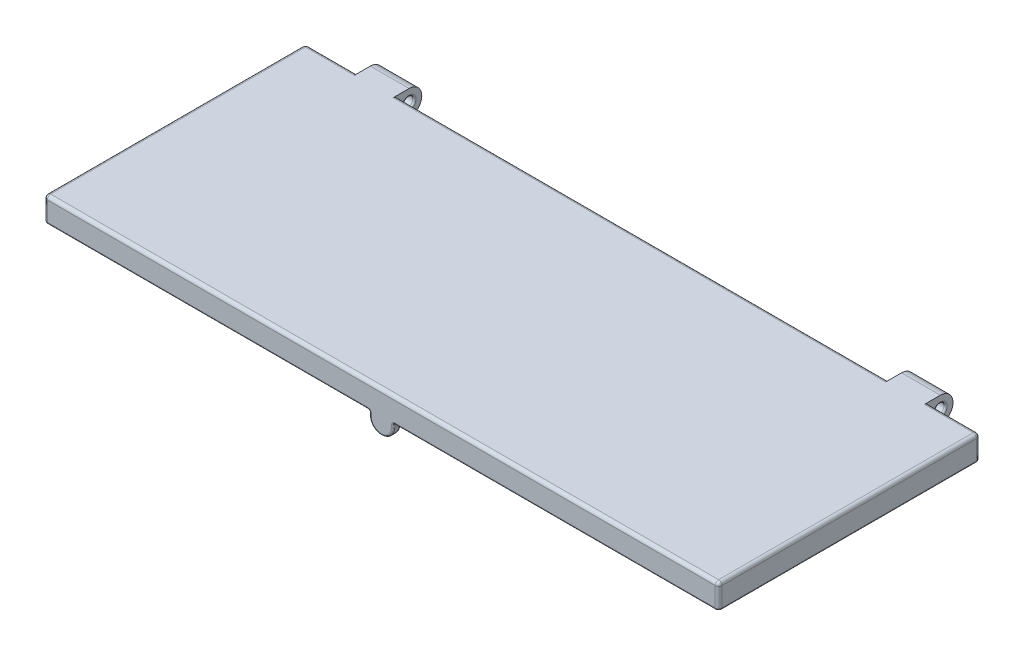
SolidWorks part; units mm, degrees
ref_plane "前视基准面" through (0, 0, 0) normal (0, 0, 1) x (1, 0, 0)
ref_plane "上视基准面" through (0, 0, 0) normal (0, 1, 0) x (1, 0, 0)
ref_plane "右视基准面" through (0, 0, 0) normal (1, 0, 0) x (0, 0, -1)
other "Configuration Table"
sketch "草图1" plane through (0, 0, 0) normal (0, 1, 0) x (1, 0, 0)
  line L0 (160, 61.2) -> (160, 0.8) construction
  line L1 (0, 0) -> (160, 0)
  line L2 (0, 0) -> (0, 62)
  line L3 (0, 62) -> (160, 62)
  line L4 (160, 0) -> (160, 62)
  line L5 (157.6, 62) -> (150.4, 62) construction
extrude "凸台-拉伸1" add sketch "草图1" along normal blind 4
ref_plane "基准面-对称" through (80, 0, 0) normal (1, 0, 0) x (0, 0, -1)
ref_plane "基准面1" through (147.6, 0, 0) normal (-1, 0, 0) x (0, 0, 1)
sketch "草图2" plane through (147.6, 0, 0) normal (-1, 0, 0) x (0, 0, 1)
  line L0 (-62, 4) -> (-65, 4)
  line L1 (-62, 0) -> (-62.6, -0.8)
  line L2 (-62, 0) -> (-62, 4)
  circle A0 centre (-65, 1) radius 1.25
  circle A1 centre (-65, 1) radius 3
  dimension "D1" = 2.5
  dimension "D2" = 6
extrude "凸台-拉伸2" add sketch "草图2" along normal blind 9.2 contours A1 L2 L0 | A1 A0 | A1 L1 L2
mirror "镜向1" about plane through (80, 0, 0) normal (1, 0, 0) of "凸台-拉伸2"
sketch "草图3" plane through (0, 0, 0) normal (0, -1, 0) x (1, 0, 0)
  line L0 (160, 0) -> (160, -62) construction
  line L1 (0, 0) -> (160, 0) construction
  line L2 (0, -62) -> (0, 0) construction
  line L3 (160, 0) -> (160, -62)
  line L4 (0, 0) -> (160, 0)
  line L5 (0, -62) -> (0, 0)
  line L6 (0, -62) -> (1.8, -62)
  line L7 (12.4, -62) -> (0, -62) construction
  line L8 (1.8, -62) -> (1.8, -1.8)
  line L9 (1.8, -1.8) -> (158.2, -1.8)
  line L10 (158.2, -1.8) -> (158.2, -62)
  line L11 (160, -62) -> (147.6, -62) construction
  line L12 (158.2, -62) -> (160, -62)
  dimension "D1" = 1.8
  dimension "D2" = 1.8
extrude "凸台-拉伸3" add sketch "草图3" along normal blind 1.8
sketch "草图4" plane through (0, 0, 0) normal (0, 0, 1) x (1, 0, 0)
  line L0 (80, -1.8) -> (80, -2.8) construction
  line L1 (160, -1.8) -> (0, -1.8) construction
  line L2 (77.2, -2.8) -> (77.2, -1.8)
  line L3 (77.2, -1.8) -> (82.8, -1.8)
  line L4 (82.8, -1.8) -> (82.8, -2.8)
  arc A0 (77.2, -2.8) -> (82.8, -2.8) centre (80, -2.8) ccw
  dimension "D1" = 2.8
  dimension "D2" = 1
extrude "凸台-拉伸4" add sketch "草图4" against normal up to surface (1.8 mm away) up to face at (80, -0.9, -1.8)
sketch "草图5" plane through (0, 0, -1.8) normal (0, 0, -1) x (-1, 0, 0)
  circle A0 centre (-80, -3) radius 0.6
  dimension "D1" = 1.2
extrude "切除-拉伸1" cut sketch "草图5" against normal blind 0.4
fillet "圆角1" radius 0.8 10 edges at (160, 4, -31) (80, 4, -62) (153.8, 4, -62) (6.2, 4, -62) (0, 4, -31) (0, 1.1, -62) (160, 1.1, -62) (160, 1.1, 0) (0, 1.1, 0) (80, 4, 0)
fillet "圆角2" radius 0.4 36 edges at (80, 0, -62) (138.4, 1, -63.75) (147.6, 1, -63.75) (7.1, 0, -62) (12.4, 1, -63.75) (21.6, 1, -63.75) (152.9, 0, -62) (1.8, 0, -31.9) (1.8, -0.9, -62) (80, 0, -1.8) (1.8, -0.9, -1.8) (158.2, 0, -31.9) (158.2, -0.9, -1.8) (158.2, -0.9, -62) (1.8, -1.8, -31.9) (39.5, -1.8, -1.8) (158.2, -1.8, -31.9) (158.7, -1.8, -62) (39, -1.8, 0) (120.5, -1.8, -1.8) (77.2, -1.8, -0.9) (82.8, -1.8, -0.9) (80, -5.6, 0) (82.8, -2.3, 0) (77.2, -2.3, 0) (80, -5.6, -1.8) (77.2, -2.3, -1.8) (82.8, -2.3, -1.8) (121, -1.8, 0) (0, -1.8, -31) (1.3, -1.8, -62) (0.2343, -1.8, -61.7657) (0.2343, -1.8, -0.2343) (160, -1.8, -31) (159.7657, -1.8, -61.7657) (159.7657, -1.8, -0.2343)
fillet "圆角3" radius 0.1 2 edges at (79.4, -3, -1.8) (79.4, -3, -1.4)
